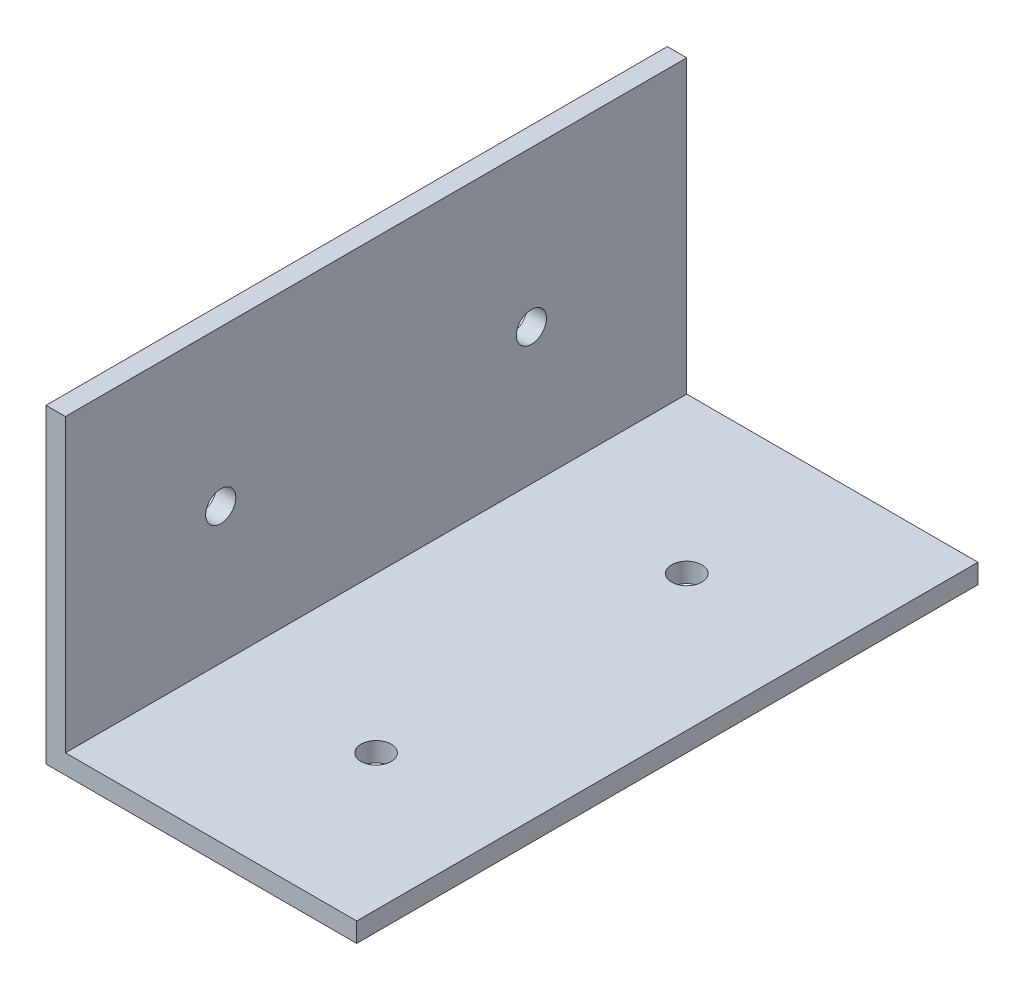
SolidWorks part; units mm, degrees
material "6061 Alloy"
ref_plane "Front Plane" through (0, 0, 0) normal (0, 0, 1) x (1, 0, 0)
ref_plane "Top Plane" through (0, 0, 0) normal (0, 1, 0) x (1, 0, 0)
ref_plane "Right Plane" through (0, 0, 0) normal (1, 0, 0) x (0, 0, -1)
sketch "Sketch1" plane through (0, 0, 0) normal (0, 0, 1) x (1, 0, 0)
  line L0 (0, 0) -> (0, 47.625)
  line L1 (0, 0) -> (47.625, 0)
  line L2 (0, 47.625) -> (-3.175, 47.625)
  line L3 (-3.175, 47.625) -> (-3.175, -3.175)
  line L4 (-3.175, -3.175) -> (47.625, -3.175)
  line L5 (47.625, -3.175) -> (47.625, 0)
  dimension "D1" = 50.8
  dimension "D2" = 50.8
  dimension "D3" = 3.175
  dimension "D4" = 3.175
extrude "Boss-Extrude1" add sketch "Sketch1" along normal blind 101.6
sketch "Sketch2" plane through (0, 0, 0) normal (0, 1, 0) x (1, 0, 0)
  line L0 (47.625, -101.6) -> (0, -101.6) construction
  line L1 (47.625, 0) -> (0, 0) construction
  line L2 (47.625, -101.6) -> (47.625, 0) construction
  circle A0 centre (25.4, -76.2) radius 2.4638
  circle A1 centre (25.4, -25.4) radius 2.4638
  point P4 (0, 0)
  dimension "D1" = 4.9276
  dimension "D2" = 4.9276
  dimension "D3" = 25.4
  dimension "D4" = 25.4
  dimension "D5" = 22.225
  dimension "D6" = 22.225
extrude "Cut-Extrude1" cut sketch "Sketch2" against normal blind 6.35
sketch "Sketch3" plane through (0, 0, 0) normal (1, 0, 0) x (0, 0, -1)
  line L0 (-101.6, 47.625) -> (0, 47.625) construction
  line L1 (0, 0) -> (0, 47.625) construction
  line L2 (-101.6, 0) -> (-101.6, 47.625) construction
  circle A0 centre (-25.4, 22.225) radius 2.4638
  circle A1 centre (-76.2, 22.225) radius 2.4638
  dimension "D1" = 4.9276
  dimension "D2" = 4.9276
  dimension "D3" = 25.4
  dimension "D4" = 25.4
  dimension "D5" = 25.4
  dimension "D6" = 25.4
extrude "Cut-Extrude2" cut sketch "Sketch3" against normal blind 6.35
